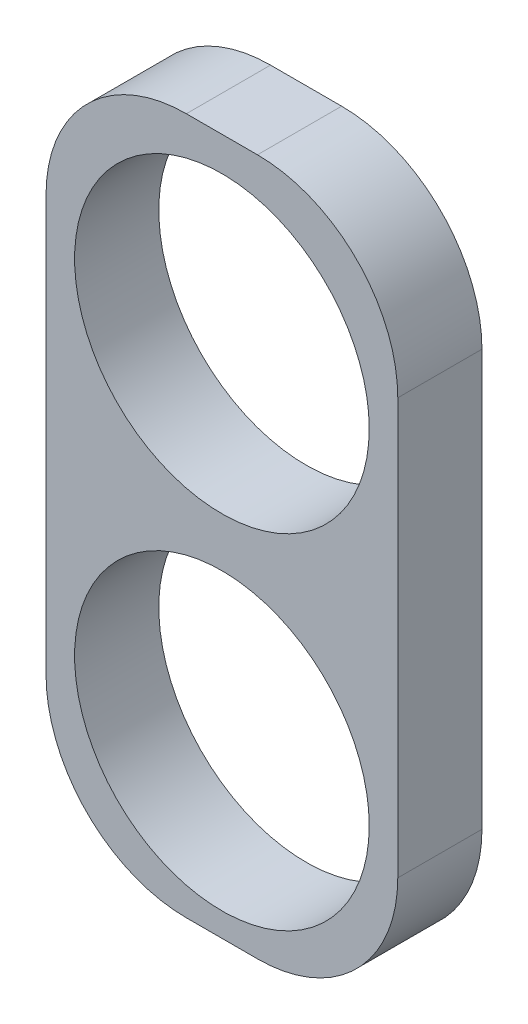
SolidWorks part; units mm, degrees
ref_plane "Front Plane" through (0, 0, 0) normal (0, 0, 1) x (1, 0, 0)
ref_plane "Top Plane" through (0, 0, 0) normal (0, 1, 0) x (1, 0, 0)
ref_plane "Right Plane" through (0, 0, 0) normal (1, 0, 0) x (0, 0, -1)
sketch "Sketch1" plane through (0, 0, 0) normal (0, 0, 1) x (1, 0, 0)
  line L1 (-2.5069, -4.9633) -> (2.5069, -4.9633)
  line L2 (-2.5069, -4.9633) -> (-2.5069, 4.9633)
  line L3 (-2.5069, 4.9633) -> (2.5069, 4.9633)
  line L4 (2.5069, -4.9633) -> (2.5069, 4.9633)
  circle A0 centre (0, 2.3781) radius 2.1
  circle A1 centre (0, -2.5241) radius 2.1
  point P0 (0, 0)
  point P10 (0, 2.3781)
  point P11 (0, -2.5241)
extrude "Boss-Extrude2" add sketch "Sketch1" along normal blind 1.2
fillet "Fillet1" radius 2 4 edges at (2.5069, -4.9633, 0.6) (-2.5069, -4.9633, 0.6) (-2.5069, 4.9633, 0.6) (2.5069, 4.9633, 0.6)
